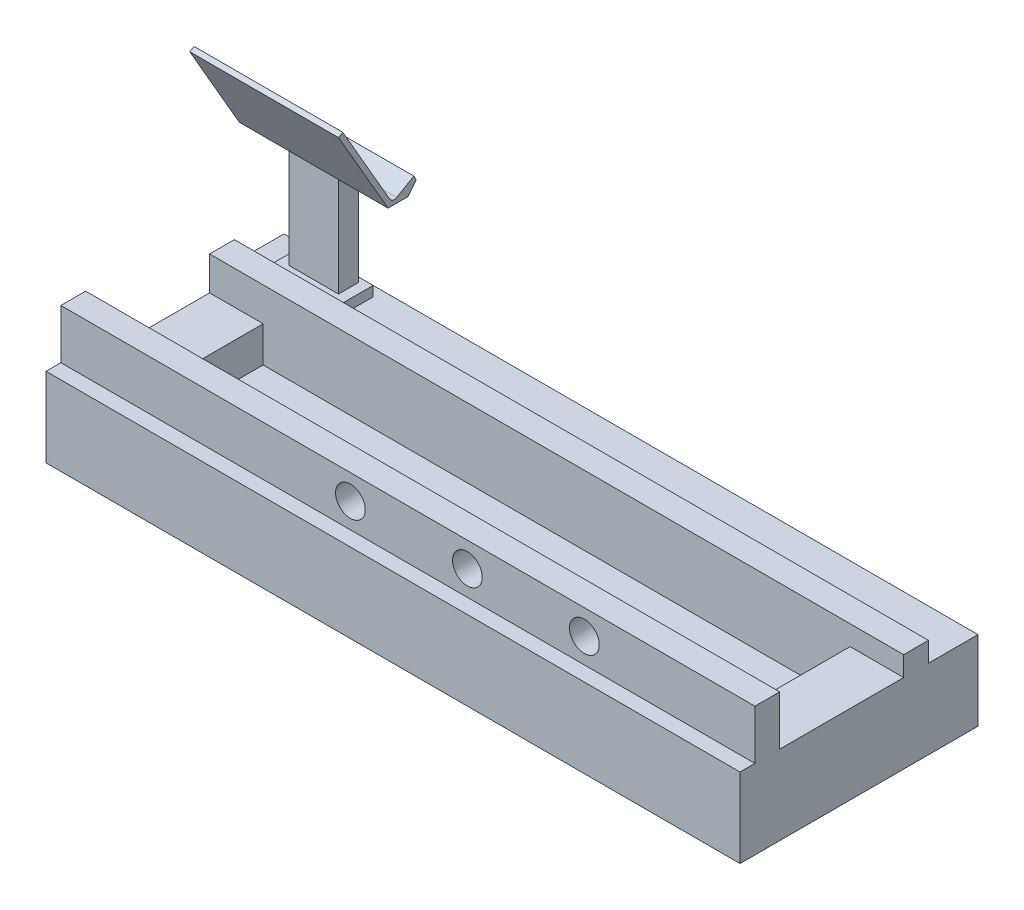
SolidWorks part; units mm, degrees
ref_plane "Front Plane" through (0, 0, 0) normal (0, 0, 1) x (1, 0, 0)
ref_plane "Top Plane" through (0, 0, 0) normal (0, 1, 0) x (1, 0, 0)
ref_plane "Right Plane" through (0, 0, 0) normal (1, 0, 0) x (0, 0, -1)
sketch "Sketch1" plane through (0, 0, 0) normal (1, 0, 0) x (0, 0, -1)
  line L0 (0, 32.9892) -> (0, -30) construction
  line L1 (-120, -30) -> (120, -30)
  line L2 (120, -30) -> (120, 50)
  line L3 (120, 50) -> (70, 50)
  line L4 (70, 50) -> (70, 70)
  line L5 (70, 70) -> (45, 70)
  line L6 (45, 70) -> (45, 0)
  line L7 (45, 0) -> (-80, 0)
  line L8 (-80, 0) -> (-80, 100)
  line L9 (-80, 100) -> (-105, 100)
  line L10 (-105, 100) -> (-105, 50)
  line L11 (-105, 50) -> (-120, 50)
  line L12 (-120, 50) -> (-120, -30)
  point P6 (0, -30)
  dimension "D1" = 240
  dimension "D2" = 80
  dimension "D3" = 50
  dimension "D4" = 25
  dimension "D5" = 25
  dimension "D6" = 15
  dimension "D7" = 50
  dimension "D8" = 20
  dimension "D9" = 100
  dimension "D10" = 80
extrude "Boss-Extrude1" add sketch "Sketch1" along normal mid plane 700
sketch "Sketch2" plane through (0, 0, 0) normal (0, 1, 0) x (1, 0, 0)
  line L0 (350, -80) -> (-350, -80) construction
  line L1 (-350, 45) -> (-296, 45)
  line L2 (-350, 45) -> (-350, -80)
  line L3 (-350, -80) -> (-296, -80)
  line L4 (-296, 45) -> (-296, -80)
  dimension "D1" = 54
extrude "Boss-Extrude2" add sketch "Sketch2" along normal blind 36
sketch "Sketch4" plane through (0, 0, 0) normal (0, 1, 0) x (1, 0, 0)
  line L0 (350, -80) -> (-350, -80) construction
  line L1 (350, 45) -> (296, 45)
  line L2 (350, 45) -> (350, -80)
  line L3 (350, -80) -> (296, -80)
  line L4 (296, 45) -> (296, -80)
  dimension "D1" = 54
extrude "Boss-Extrude3" add sketch "Sketch4" along normal blind 50
sketch "Sketch5" plane through (0, 0, 80) normal (0, 0, -1) x (-1, 0, 0)
  circle A0 centre (-178, 75) radius 15
  circle A1 centre (-60, 75) radius 15
  circle A2 centre (58, 75) radius 15
  circle A4 centre (176, 75) radius 15
  point P0 (-178, 75)
  dimension "D3" = 30
  dimension "D4" = 4
  dimension "D5" = 118
  dimension "D1" = 118
  dimension "D2" = 25
extrude "Cut-Extrude1" cut sketch "Sketch5" against normal blind 25
sketch "Sketch6" plane through (0, 50, 0) normal (0, 1, 0) x (1, 0, 0)
  line L0 (350, 120) -> (-350, 120) construction
  line L1 (-320, 110) -> (-250, 110)
  line L2 (-320, 110) -> (-320, 80)
  line L3 (-320, 80) -> (-250, 80)
  line L4 (-250, 110) -> (-250, 80)
  line L5 (350, 70) -> (-350, 70) construction
  line L6 (350, 120) -> (350, 70) construction
  dimension "D1" = 10
  dimension "D2" = 30
  dimension "D3" = 10
  dimension "D4" = 600
extrude "Boss-Extrude4" add sketch "Sketch6" along normal blind 10
sketch "Sketch7" plane through (0, 60, 0) normal (0, 1, 0) x (1, 0, 0)
  line L0 (-320, 110) -> (-320, 80) construction
  line L1 (-310, 105) -> (-260, 105)
  line L2 (-310, 105) -> (-310, 85)
  line L3 (-310, 85) -> (-260, 85)
  line L4 (-260, 105) -> (-260, 85)
  line L5 (-250, 80) -> (-250, 110) construction
  line L6 (-250, 110) -> (-320, 110) construction
  line L7 (-320, 80) -> (-250, 80) construction
  point P4 (-310, 95)
  dimension "D1" = 10
  dimension "D2" = 10
  dimension "D3" = 5
  dimension "D4" = 5
extrude "Boss-Extrude5" add sketch "Sketch7" along normal blind 100
ref_plane "Plane1" through (-285, 0, 0) normal (-1, 0, 0) x (0, 0, 1)
sketch "Sketch10" plane through (-285, 0, 0) normal (-1, 0, 0) x (0, 0, 1)
  line L0 (-105, 160) -> (-85, 160)
  line L1 (-85, 160) -> (-35, 246.6025)
  line L2 (-35, 246.6025) -> (-39.3301, 249.1025)
  line L3 (-39.3301, 249.1025) -> (-86.8301, 166.8301)
  line L4 (-93.6603, 165) -> (-110.9808, 175)
  line L5 (-110.9808, 175) -> (-113.4808, 170.6699)
  line L6 (-113.4808, 170.6699) -> (-105, 160)
  line L7 (-157.8411, 160) -> (-32.1589, 160) construction
  arc A0 (-86.8301, 166.8301) -> (-93.6603, 165) centre (-91.1603, 169.3301) cw
  point P13 (-95, 160)
  point P14 (-89.3301, 162.5)
  dimension "D9" = 5
  dimension "D1" = 21.521
  dimension "D2" = 5
  dimension "D3" = 5
  dimension "D4" = 25
  dimension "D5" = 60
  dimension "D6" = 100
  dimension "D7" = 100
  dimension "D8" = 5
extrude "Boss-Extrude6" add sketch "Sketch10" along normal mid plane 150
